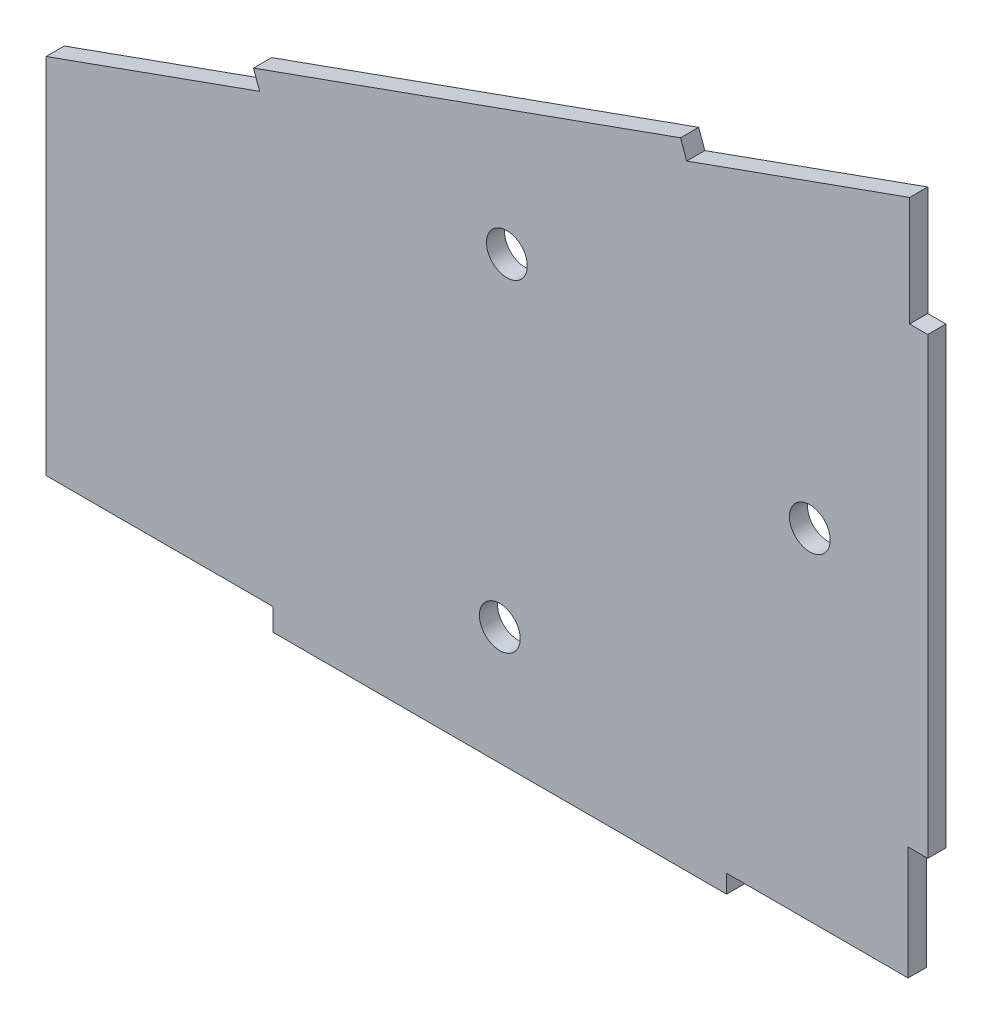
SolidWorks part; units mm, degrees
ref_plane "前视基准面" through (0, 0, 0) normal (0, 0, 1) x (1, 0, 0)
ref_plane "上视基准面" through (0, 0, 0) normal (0, 1, 0) x (1, 0, 0)
ref_plane "右视基准面" through (0, 0, 0) normal (1, 0, 0) x (0, 0, -1)
sketch "草图2" plane through (0, 0, 0) normal (0, 0, 1) x (1, 0, 0)
  line L0 (30.2242, 24.6802) -> (30.2242, 36.7602)
  line L3 (-64.9407, -37.3698) -> (-39.9407, -37.3698)
  line L6 (-64.9407, 2.6302) -> (-64.9407, -37.3698)
  line L8 (-39.9407, -37.3698) -> (-39.9407, -39.8198)
  line L9 (-39.9407, -39.8198) -> (10.0593, -39.8198)
  line L10 (10.0593, -37.8198) -> (10.0593, -39.8198)
  line L13 (30.2242, 24.6802) -> (32.2242, 24.6802)
  line L16 (32.2242, 24.6802) -> (32.2242, -25.3198)
  line L19 (30.2242, 36.7602) -> (5.6564, 27.9492)
  line L29 (-41.4083, 11.0699) -> (-42.0835, 12.9525)
  line L30 (5.6564, 27.9492) -> (4.9812, 29.8318)
  line L31 (-42.0835, 12.9525) -> (4.9812, 29.8318)
  line L33 (10.0593, -37.8198) -> (30.0593, -37.8198)
  line L36 (-41.4083, 11.0699) -> (-64.9407, 2.6302)
  line L43 (30.0593, -37.8198) -> (30.0593, -25.3198)
  line L44 (30.0593, -25.3198) -> (32.2242, -25.3198)
  point P167 (-55.0804, -13.4175)
  point P184 (-14.9407, -38.3698)
  point P197 (41.9196, -11.6019)
  point P204 (-22.6976, 6.5825)
  dimension "D2" = 50
  dimension "D3" = 40
  dimension "D4" = 25
  dimension "D5" = 20
  dimension "D6" = 25
  dimension "D7" = 26.1
  dimension "D8" = 2
  dimension "D9" = 12.5
  dimension "D10" = 2
  dimension "D11" = 2
  dimension "D12" = 12.08
  dimension "D13" = 50
  dimension "D14" = 50
extrude "凸台-拉伸1" add sketch "草图2" along normal blind 2
sketch "草图3" plane through (0, 0, 0) normal (0, 0, 1) x (1, 0, 0)
  line L0 (-39.9407, -39.8198) -> (10.0593, -39.8198) construction
  line L1 (4.9812, 29.8318) -> (-42.0835, 12.9525) construction
  line L2 (-20.8506, 27.8037) -> (-13.2732, 6.6757) construction
  line L3 (-41.4083, 11.0699) -> (-64.9407, 2.6302) construction
  line L4 (32.2242, -25.3198) -> (32.2242, 24.6802) construction
  line L5 (48.3589, -0.3198) -> (9.259, -0.3198) construction
  line L6 (30.2242, 24.6802) -> (30.2242, 36.7602) construction
  line L7 (10.0593, -37.8198) -> (30.0593, -37.8198) construction
  circle A0 centre (-14.1625, 9.1553) radius 2.25
  circle A1 centre (19.2242, -0.3198) radius 2.25
  circle A2 centre (-14.9407, -26.8198) radius 2.25
  point P0 (-14.9407, -39.8198)
  point P1 (-18.5511, 21.3921)
  point P13 (32.2242, -0.3198)
  dimension "D1" = 4.5
  dimension "D3" = 4.5
  dimension "D5" = 4.5
  dimension "D2" = 11
  dimension "D4" = 11
  dimension "D6" = 11
extrude "切除-拉伸1" cut sketch "草图3" against normal blind 10 and the other way blind 2
